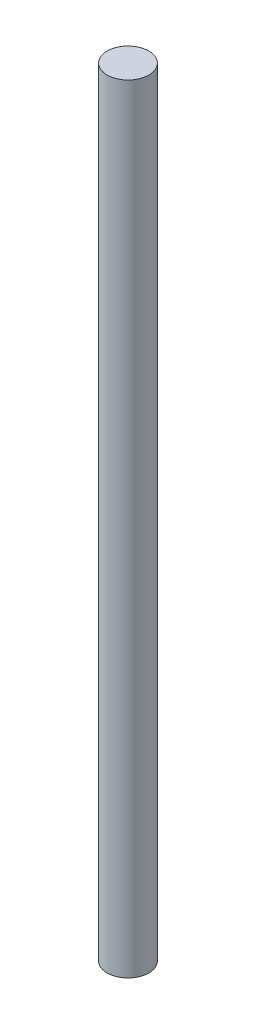
SolidWorks part; units mm, degrees
ref_plane "Front Plane" through (0, 0, 0) normal (0, 0, 1) x (1, 0, 0)
ref_plane "Top Plane" through (0, 0, 0) normal (0, 1, 0) x (1, 0, 0)
ref_plane "Right Plane" through (0, 0, 0) normal (1, 0, 0) x (0, 0, -1)
sketch "Sketch1" plane through (0, 0, 0) normal (0, 1, 0) x (1, 0, 0)
  circle A0 centre (0, 0) radius 4.7625
  dimension "D1" = 9.525
extrude "Boss-Extrude1" add sketch "Sketch1" along normal blind 177.8
